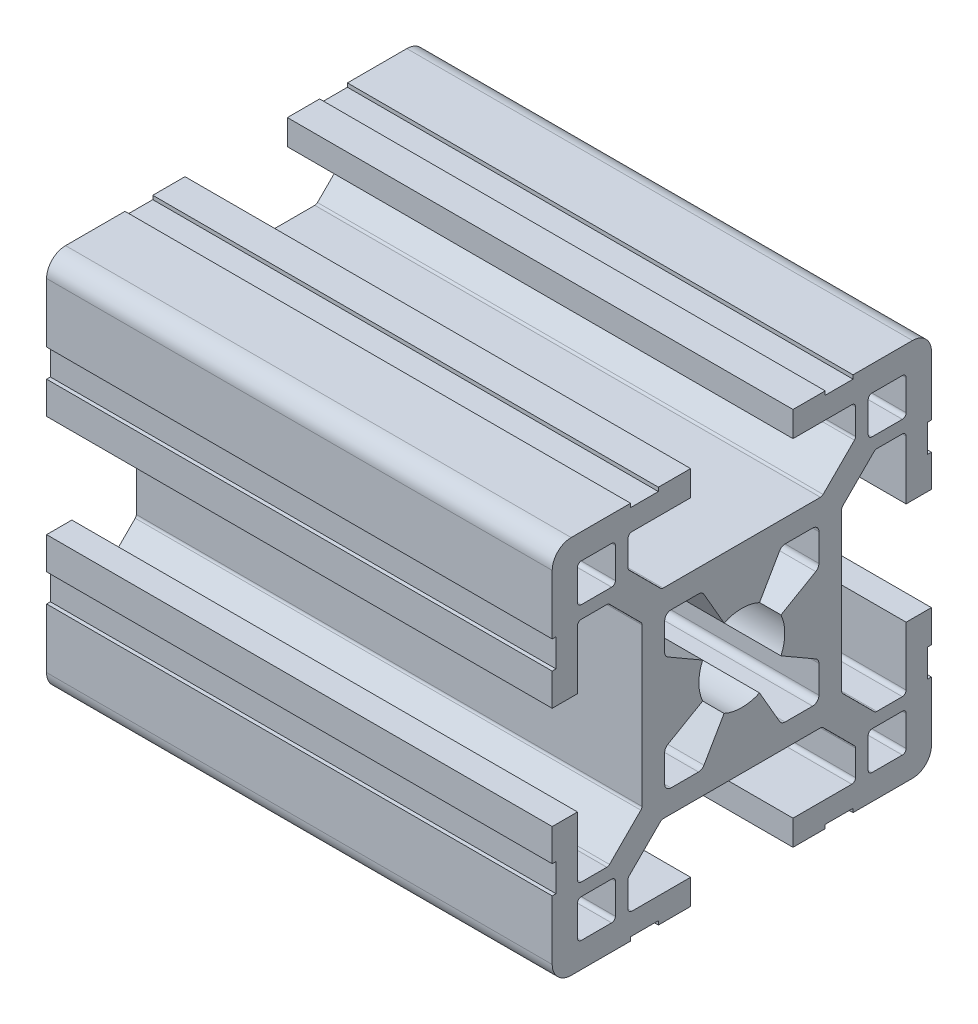
SolidWorks part; units mm, degrees
material "6063-T5"
ref_plane "Plano frontal" through (0, 0, 0) normal (0, 0, 1) x (1, 0, 0)
ref_plane "Plano superior" through (0, 0, 0) normal (0, 1, 0) x (1, 0, 0)
ref_plane "Plano direito" through (0, 0, 0) normal (1, 0, 0) x (0, 0, -1)
sketch "Esboço1" plane through (0, 0, 0) normal (0, 0, 1) x (1, 0, 0)
  line L0 (0, 0) -> (40, 0)
  dimension "D1" = 40
other "Quadrado PF30-11 - PERFIL 3030 CENTRO M8(1)"
ref_plane "Plano1" through (0, 0, 0) normal (1, 0, 0) x (0, 1, 0)
sketch "Sketch1" plane through (0, 0, 0) normal (1, 0, 0) x (0, 1, 0)
  line L0 (-6.1, -3.4254) -> (-6.1, -5.6)
  line L1 (-5.6, -6.1) -> (-3.4254, -6.1)
  line L2 (3.4254, -6.1) -> (5.6, -6.1)
  line L3 (6.1, -5.6) -> (6.1, -3.4254)
  line L4 (6.1, 3.4254) -> (6.1, 5.6)
  line L5 (5.6, 6.1) -> (3.4254, 6.1)
  line L6 (-3.4254, 6.1) -> (-5.6, 6.1)
  line L7 (-6.1, 5.6) -> (-6.1, 3.4254)
  line L8 (15, 6.6) -> (14.7, 6.6)
  line L9 (5.85, -2.9924) -> (3.097, -1.403)
  line L10 (10, 12.7) -> (10, 10.3)
  line L11 (13, -12.7) -> (13, -10.3)
  line L12 (-10.3, -10) -> (-12.7, -10)
  line L13 (-13, 12.7) -> (-13, 10.3)
  line L14 (3.097, 1.403) -> (5.85, 2.9924)
  line L15 (2.9924, 5.85) -> (1.403, 3.097)
  line L16 (-1.403, 3.097) -> (-2.9924, 5.85)
  line L17 (-5.85, 2.9924) -> (-3.097, 1.403)
  line L18 (-3.097, -1.403) -> (-5.85, -2.9924)
  line L19 (-2.9924, -5.85) -> (-1.403, -3.097)
  line L20 (1.403, -3.097) -> (2.9924, -5.85)
  line L21 (10.3, 10) -> (12.7, 10)
  line L22 (13, 10.3) -> (13, 12.7)
  line L23 (12.7, 13) -> (10.3, 13)
  line L24 (12.7, -10) -> (10.3, -10)
  line L25 (10, -10.3) -> (10, -12.7)
  line L26 (10.3, -13) -> (12.7, -13)
  line L27 (-13, -10.3) -> (-13, -12.7)
  line L28 (-12.7, -13) -> (-10.3, -13)
  line L29 (-10, -12.7) -> (-10, -10.3)
  line L30 (-12.7, 10) -> (-10.3, 10)
  line L31 (-10, 10.3) -> (-10, 12.7)
  line L32 (-10.3, 13) -> (-12.7, 13)
  line L33 (15, 4.05) -> (15, 6.6)
  line L34 (13, 4.05) -> (15, 4.05)
  line L35 (13, 8.7) -> (13, 4.05)
  line L36 (10.6799, 9) -> (12.7, 9)
  line L37 (7.9879, 6.4322) -> (10.4678, 8.9121)
  line L38 (7.9, -6.2201) -> (7.9, 6.2201)
  line L39 (10.4678, -8.9121) -> (7.9879, -6.4322)
  line L40 (12.7, -9) -> (10.6799, -9)
  line L41 (13, -4.05) -> (13, -8.7)
  line L42 (15, -4.05) -> (13, -4.05)
  line L43 (15, -6.6) -> (15, -4.05)
  line L44 (14.7, -6.6) -> (15, -6.6)
  line L45 (14.7, -8.8) -> (14.7, -6.6)
  line L46 (15, -8.8) -> (14.7, -8.8)
  line L47 (15, -13.5) -> (15, -8.8)
  line L48 (8.8, -15) -> (13.5, -15)
  line L49 (8.8, -14.7) -> (8.8, -15)
  line L50 (6.6, -14.7) -> (8.8, -14.7)
  line L51 (6.6, -15) -> (6.6, -14.7)
  line L52 (4.05, -15) -> (6.6, -15)
  line L53 (4.05, -13) -> (4.05, -15)
  line L54 (8.7, -13) -> (4.05, -13)
  line L55 (9, -10.6799) -> (9, -12.7)
  line L56 (6.4322, -7.9879) -> (8.9121, -10.4678)
  line L57 (-6.2201, -7.9) -> (6.2201, -7.9)
  line L58 (-8.9121, -10.4678) -> (-6.4322, -7.9879)
  line L59 (-9, -12.7) -> (-9, -10.6799)
  line L60 (-4.05, -13) -> (-8.7, -13)
  line L61 (-4.05, -15) -> (-4.05, -13)
  line L62 (-6.6, -15) -> (-4.05, -15)
  line L63 (-6.6, -14.7) -> (-6.6, -15)
  line L64 (-8.8, -14.7) -> (-6.6, -14.7)
  line L65 (-8.8, -15) -> (-8.8, -14.7)
  line L66 (-13.5, -15) -> (-8.8, -15)
  line L67 (-15, -8.8) -> (-15, -13.5)
  line L68 (-14.7, -8.8) -> (-15, -8.8)
  line L69 (-14.7, -6.6) -> (-14.7, -8.8)
  line L70 (-15, -6.6) -> (-14.7, -6.6)
  line L71 (-15, -4.05) -> (-15, -6.6)
  line L72 (-13, -4.05) -> (-15, -4.05)
  line L73 (-13, -8.7) -> (-13, -4.05)
  line L74 (-10.6799, -9) -> (-12.7, -9)
  line L75 (-7.9879, -6.4322) -> (-10.4678, -8.9121)
  line L76 (-7.9, 6.2201) -> (-7.9, -6.2201)
  line L77 (-10.4678, 8.9121) -> (-7.9879, 6.4322)
  line L78 (-12.7, 9) -> (-10.6799, 9)
  line L79 (-13, 4.05) -> (-13, 8.7)
  line L80 (-15, 4.05) -> (-13, 4.05)
  line L81 (-15, 6.6) -> (-15, 4.05)
  line L82 (-14.7, 6.6) -> (-15, 6.6)
  line L83 (-14.7, 8.8) -> (-14.7, 6.6)
  line L84 (-15, 8.8) -> (-14.7, 8.8)
  line L85 (-15, 13.5) -> (-15, 8.8)
  line L86 (-8.8, 15) -> (-13.5, 15)
  line L87 (-8.8, 14.7) -> (-8.8, 15)
  line L88 (-6.6, 14.7) -> (-8.8, 14.7)
  line L89 (-6.6, 15) -> (-6.6, 14.7)
  line L90 (-4.05, 15) -> (-6.6, 15)
  line L91 (-4.05, 13) -> (-4.05, 15)
  line L92 (-8.7, 13) -> (-4.05, 13)
  line L93 (-9, 10.6799) -> (-9, 12.7)
  line L94 (-6.4322, 7.9879) -> (-8.9121, 10.4678)
  line L95 (6.2201, 7.9) -> (-6.2201, 7.9)
  line L96 (8.9121, 10.4678) -> (6.4322, 7.9879)
  line L97 (9, 12.7) -> (9, 10.6799)
  line L98 (4.05, 13) -> (8.7, 13)
  line L99 (4.05, 15) -> (4.05, 13)
  line L100 (6.6, 15) -> (4.05, 15)
  line L101 (6.6, 14.7) -> (6.6, 15)
  line L102 (8.8, 14.7) -> (6.6, 14.7)
  line L103 (8.8, 15) -> (8.8, 14.7)
  line L104 (13.5, 15) -> (8.8, 15)
  line L105 (15, 8.8) -> (15, 13.5)
  line L106 (14.7, 8.8) -> (15, 8.8)
  line L107 (14.7, 6.6) -> (14.7, 8.8)
  arc A0 (-5.85, -2.9924) -> (-6.1, -3.4254) centre (-5.6, -3.4254) ccw
  arc A1 (-6.1, -5.6) -> (-5.6, -6.1) centre (-5.6, -5.6) ccw
  arc A2 (-3.4254, -6.1) -> (-2.9924, -5.85) centre (-3.4254, -5.6) ccw
  arc A3 (2.9924, -5.85) -> (3.4254, -6.1) centre (3.4254, -5.6) ccw
  arc A4 (5.6, -6.1) -> (6.1, -5.6) centre (5.6, -5.6) ccw
  arc A5 (6.1, -3.4254) -> (5.85, -2.9924) centre (5.6, -3.4254) ccw
  arc A6 (5.85, 2.9924) -> (6.1, 3.4254) centre (5.6, 3.4254) ccw
  arc A7 (6.1, 5.6) -> (5.6, 6.1) centre (5.6, 5.6) ccw
  arc A8 (3.4254, 6.1) -> (2.9924, 5.85) centre (3.4254, 5.6) ccw
  arc A9 (-2.9924, 5.85) -> (-3.4254, 6.1) centre (-3.4254, 5.6) ccw
  arc A10 (-5.6, 6.1) -> (-6.1, 5.6) centre (-5.6, 5.6) ccw
  arc A11 (-6.1, 3.4254) -> (-5.85, 2.9924) centre (-5.6, 3.4254) ccw
  arc A12 (3.097, -1.403) -> (3.097, 1.403) centre (0, 0) ccw
  arc A13 (1.403, 3.097) -> (-1.403, 3.097) centre (0, 0) ccw
  arc A14 (-3.097, 1.403) -> (-3.097, -1.403) centre (0, 0) ccw
  arc A15 (-1.403, -3.097) -> (1.403, -3.097) centre (0, 0) ccw
  arc A16 (10, 10.3) -> (10.3, 10) centre (10.3, 10.3) ccw
  arc A17 (12.7, 10) -> (13, 10.3) centre (12.7, 10.3) ccw
  arc A18 (13, 12.7) -> (12.7, 13) centre (12.7, 12.7) ccw
  arc A19 (10.3, 13) -> (10, 12.7) centre (10.3, 12.7) ccw
  arc A20 (13, -10.3) -> (12.7, -10) centre (12.7, -10.3) ccw
  arc A21 (10.3, -10) -> (10, -10.3) centre (10.3, -10.3) ccw
  arc A22 (10, -12.7) -> (10.3, -13) centre (10.3, -12.7) ccw
  arc A23 (12.7, -13) -> (13, -12.7) centre (12.7, -12.7) ccw
  arc A24 (-12.7, -10) -> (-13, -10.3) centre (-12.7, -10.3) ccw
  arc A25 (-13, -12.7) -> (-12.7, -13) centre (-12.7, -12.7) ccw
  arc A26 (-10.3, -13) -> (-10, -12.7) centre (-10.3, -12.7) ccw
  arc A27 (-10, -10.3) -> (-10.3, -10) centre (-10.3, -10.3) ccw
  arc A28 (-13, 10.3) -> (-12.7, 10) centre (-12.7, 10.3) ccw
  arc A29 (-10.3, 10) -> (-10, 10.3) centre (-10.3, 10.3) ccw
  arc A30 (-10, 12.7) -> (-10.3, 13) centre (-10.3, 12.7) ccw
  arc A31 (-12.7, 13) -> (-13, 12.7) centre (-12.7, 12.7) ccw
  arc A32 (13, 8.7) -> (12.7, 9) centre (12.7, 8.7) ccw
  arc A33 (10.6799, 9) -> (10.4678, 8.9121) centre (10.6799, 8.7) ccw
  arc A34 (7.9879, 6.4322) -> (7.9, 6.2201) centre (8.2, 6.2201) ccw
  arc A35 (7.9, -6.2201) -> (7.9879, -6.4322) centre (8.2, -6.2201) ccw
  arc A36 (10.4678, -8.9121) -> (10.6799, -9) centre (10.6799, -8.7) ccw
  arc A37 (12.7, -9) -> (13, -8.7) centre (12.7, -8.7) ccw
  arc A38 (13.5, -15) -> (15, -13.5) centre (13.5, -13.5) ccw
  arc A39 (8.7, -13) -> (9, -12.7) centre (8.7, -12.7) ccw
  arc A40 (9, -10.6799) -> (8.9121, -10.4678) centre (8.7, -10.6799) ccw
  arc A41 (6.4322, -7.9879) -> (6.2201, -7.9) centre (6.2201, -8.2) ccw
  arc A42 (-6.2201, -7.9) -> (-6.4322, -7.9879) centre (-6.2201, -8.2) ccw
  arc A43 (-8.9121, -10.4678) -> (-9, -10.6799) centre (-8.7, -10.6799) ccw
  arc A44 (-9, -12.7) -> (-8.7, -13) centre (-8.7, -12.7) ccw
  arc A45 (-15, -13.5) -> (-13.5, -15) centre (-13.5, -13.5) ccw
  arc A46 (-13, -8.7) -> (-12.7, -9) centre (-12.7, -8.7) ccw
  arc A47 (-10.6799, -9) -> (-10.4678, -8.9121) centre (-10.6799, -8.7) ccw
  arc A48 (-7.9879, -6.4322) -> (-7.9, -6.2201) centre (-8.2, -6.2201) ccw
  arc A49 (-7.9, 6.2201) -> (-7.9879, 6.4322) centre (-8.2, 6.2201) ccw
  arc A50 (-10.4678, 8.9121) -> (-10.6799, 9) centre (-10.6799, 8.7) ccw
  arc A51 (-12.7, 9) -> (-13, 8.7) centre (-12.7, 8.7) ccw
  arc A52 (-13.5, 15) -> (-15, 13.5) centre (-13.5, 13.5) ccw
  arc A53 (-8.7, 13) -> (-9, 12.7) centre (-8.7, 12.7) ccw
  arc A54 (-9, 10.6799) -> (-8.9121, 10.4678) centre (-8.7, 10.6799) ccw
  arc A55 (-6.4322, 7.9879) -> (-6.2201, 7.9) centre (-6.2201, 8.2) ccw
  arc A56 (6.2201, 7.9) -> (6.4322, 7.9879) centre (6.2201, 8.2) ccw
  arc A57 (8.9121, 10.4678) -> (9, 10.6799) centre (8.7, 10.6799) ccw
  arc A58 (9, 12.7) -> (8.7, 13) centre (8.7, 12.7) ccw
  arc A59 (15, 13.5) -> (13.5, 15) centre (13.5, 13.5) ccw
  point P1 (0, 0)
  point P2 (0, 0)
  point P3 (-15, -15)
  point P4 (0, -15)
  point P5 (-15, 0)
  point P230 (-15, 15)
  point P231 (0, 15)
  point P232 (15, 15)
  point P233 (15, 0)
  point P234 (15, -15)
  point P235 (0, -15)
  point P236 (-15, -15)
  point P237 (-15, 0)
  point P238 (0, 0)
  point P239 (0, 0)
